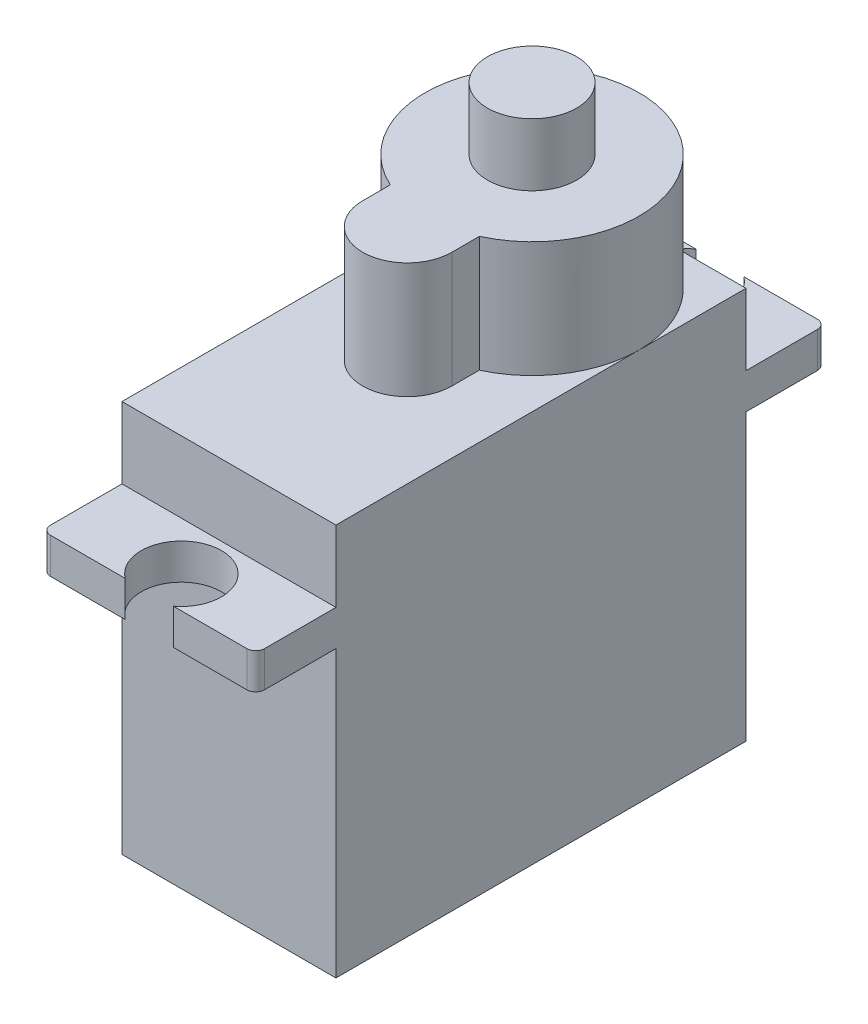
SolidWorks part; units mm, degrees
ref_plane "Front Plane" through (0, 0, 0) normal (0, 0, 1) x (1, 0, 0)
ref_plane "Top Plane" through (0, 0, 0) normal (0, 1, 0) x (1, 0, 0)
ref_plane "Right Plane" through (0, 0, 0) normal (1, 0, 0) x (0, 0, -1)
sketch "Sketch1" plane through (0, 0, 0) normal (0, 1, 0) x (1, 0, 0)
  line L1 (45.3144, -93.1516) -> (57.3144, -93.1516)
  line L2 (45.3144, -93.1516) -> (45.3144, -116.1516)
  line L3 (45.3144, -116.1516) -> (57.3144, -116.1516)
  line L4 (57.3144, -93.1516) -> (57.3144, -116.1516)
  dimension "D1" = 23
  dimension "D2" = 12
sketch "Sketch3" plane through (0, 0, 0) normal (0, 1, 0) x (1, 0, 0)
  line L0 (45.3144, -93.1516) -> (57.3144, -93.1516) construction
  line L1 (57.3144, -93.1516) -> (57.3144, -116.1516) construction
  line L2 (45.3144, -93.1516) -> (45.3144, -116.1516) construction
  line L5 (48.8144, -106.1516) -> (48.8144, -104.606)
  line L6 (53.8144, -104.606) -> (53.8144, -106.1516)
  arc A0 (53.8144, -104.606) -> (48.8144, -104.606) centre (51.3144, -99.1516) ccw
  arc A1 (48.8144, -106.1516) -> (53.8144, -106.1516) centre (51.3144, -106.1516) ccw
  dimension "D1" = 12
  dimension "D4" = 5
  dimension "D2" = 6
  dimension "D3" = 6
  dimension "D5" = 6
  dimension "D6" = 13
sketch "Sketch4" plane through (0, 0, 0) normal (0, 1, 0) x (1, 0, 0)
  line L0 (57.3144, -93.1516) -> (57.3144, -116.1516) construction
  line L1 (45.3144, -93.1516) -> (57.3144, -93.1516) construction
  circle A0 centre (51.3144, -99.1516) radius 2.5
  dimension "D3" = 5
  dimension "D1" = 6
  dimension "D2" = 6
extrude "Boss-Extrude2" add sketch "Sketch4" along normal blind 32
extrude "Boss-Extrude3" add sketch "Sketch3" along normal blind 28.5
extrude "Boss-Extrude4" add sketch "Sketch1" along normal blind 22
sketch3d "3DSketch3" plane through (0, 0, 0) normal (0, 0, 1) x (1, 0, 0)
  dimension "D1" = 16
sketch "Sketch7" plane through (0, 16, 0) normal (0, 1, 0) x (1, 0, 0)
  line L0 (52.6945, -120.6516) -> (57.3144, -120.6516)
  line L1 (45.3144, -116.1516) -> (57.3144, -116.1516)
  line L2 (45.3144, -116.1516) -> (45.3144, -120.6516)
  line L3 (45.3144, -120.6516) -> (49.9945, -120.6516)
  line L4 (57.3144, -116.1516) -> (57.3144, -120.6516)
  line L5 (45.3144, -104.6516) -> (57.3144, -104.6516) construction
  line L6 (45.3144, -93.1516) -> (45.3144, -116.1516) construction
  line L7 (57.3144, -93.1516) -> (57.3144, -116.1516) construction
  line L8 (45.3144, -93.1516) -> (57.3144, -93.1516)
  line L9 (57.3144, -93.1516) -> (57.3144, -88.6516)
  line L10 (52.6945, -88.6516) -> (57.3144, -88.6516)
  line L11 (45.3144, -88.6516) -> (49.9945, -88.6516)
  line L12 (45.3144, -93.1516) -> (45.3144, -88.6516)
  arc A0 (52.6945, -120.6516) -> (49.9945, -120.6516) centre (51.3445, -118.8516) ccw
  arc A1 (52.6945, -88.6516) -> (49.9945, -88.6516) centre (51.3445, -90.4516) cw
  dimension "D1" = 4.5
  dimension "D2" = 1.8
extrude "Boss-Extrude6" add sketch "Sketch7" along normal blind 2
fillet "Fillet2" radius 0.5 4 edges at (45.3144, 17, 120.6516) (57.3144, 17, 120.6516) (57.3144, 17, 88.6516) (45.3144, 17, 88.6516)
